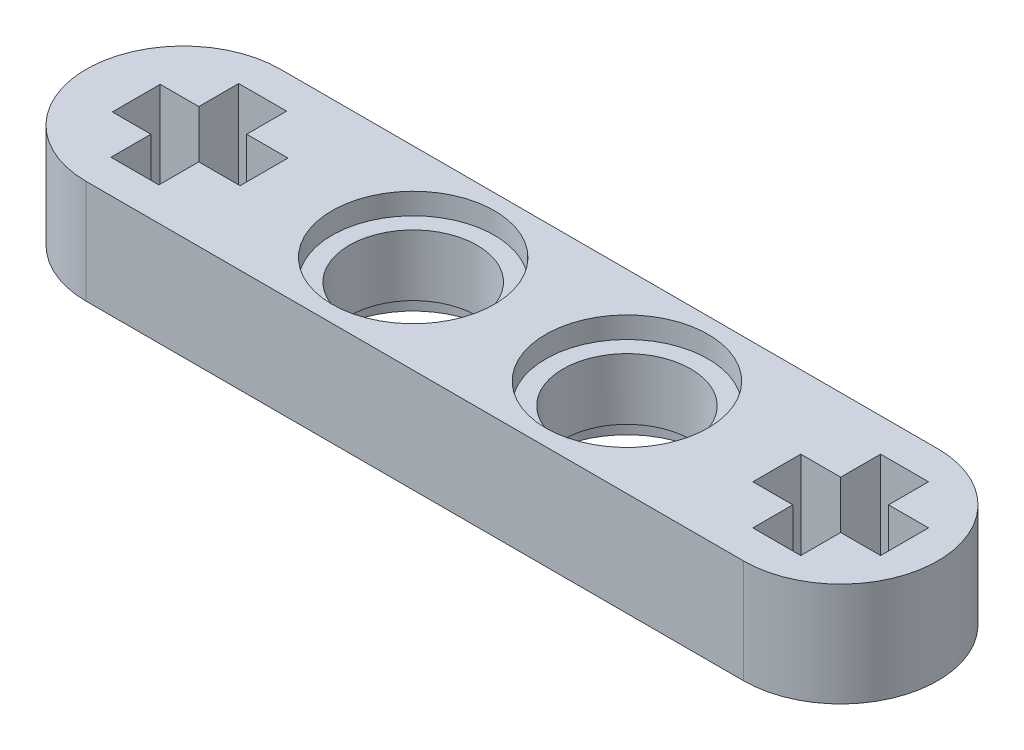
SolidWorks part; units mm, degrees
ref_plane "Front Plane" through (0, 0, 0) normal (0, 0, 1) x (1, 0, 0)
ref_plane "Top Plane" through (0, 0, 0) normal (0, 1, 0) x (1, 0, 0)
ref_plane "Right Plane" through (0, 0, 0) normal (1, 0, 0) x (0, 0, -1)
sketch "Sketch1" plane through (0, 0, 0) normal (0, 1, 0) x (1, 0, 0)
  line L0 (-12.665, 0) -> (12.035, 0) construction
  line L1 (-55, 0) -> (55, 0) construction
  line L2 (-12.665, 3.65) -> (12.035, 3.65)
  line L3 (-12.665, -3.65) -> (12.035, -3.65)
  line L4 (-16.315, 0) -> (-16.315, -5.5699) construction
  line L5 (-14.435, 0) -> (-14.435, -5.5699) construction
  line L6 (11.135, 2.4) -> (11.135, 0.9)
  line L7 (11.135, 2.4) -> (12.935, 2.4)
  line L8 (11.135, -2.4) -> (12.935, -2.4)
  line L9 (12.935, 2.4) -> (12.935, 0.9)
  line L10 (11.135, 2.4) -> (12.935, -2.4) construction
  line L11 (11.135, -2.4) -> (12.935, 2.4) construction
  line L12 (14.435, -0.9) -> (12.935, -0.9)
  line L13 (14.435, -0.9) -> (14.435, 0.9)
  line L14 (9.635, -0.9) -> (9.635, 0.9)
  line L15 (14.435, 0.9) -> (12.935, 0.9)
  line L16 (14.435, -0.9) -> (9.635, 0.9) construction
  line L17 (9.635, -0.9) -> (14.435, 0.9) construction
  line L18 (11.135, 0.9) -> (9.635, 0.9)
  line L19 (11.135, -0.9) -> (9.635, -0.9)
  line L20 (11.135, -0.9) -> (11.135, -2.4)
  line L21 (12.935, -0.9) -> (12.935, -2.4)
  line L34 (-12.985, 2.4011) -> (-12.985, 0.9011)
  line L35 (-12.985, 2.4011) -> (-11.185, 2.4011)
  line L36 (-12.985, -2.3989) -> (-11.185, -2.3989)
  line L37 (-11.185, 2.4011) -> (-11.185, 0.9011)
  line L38 (-9.6331, -0.8989) -> (-11.185, -0.8989)
  line L39 (-9.6331, -0.8989) -> (-9.6331, 0.9011)
  line L40 (-14.4331, -0.8989) -> (-14.4331, 0.9011)
  line L41 (-9.6331, 0.9011) -> (-11.185, 0.9011)
  line L42 (-12.985, 0.9011) -> (-14.4331, 0.9011)
  line L43 (-12.985, -0.8989) -> (-14.4331, -0.8989)
  line L44 (-12.985, -0.8989) -> (-12.985, -2.3989)
  line L45 (-11.185, -0.8989) -> (-11.185, -2.3989)
  line L46 (-12.985, 0.9011) -> (-11.185, -0.8989) construction
  line L47 (-12.085, 0.0011) -> (-11.185, 0.9011) construction
  arc A0 (-12.665, 3.65) -> (-12.665, -3.65) centre (-12.665, 0) ccw
  arc A1 (12.035, -3.65) -> (12.035, 3.65) centre (12.035, 0) ccw
  circle A2 centre (-4.045, 0.018) radius 2.4
  circle A3 centre (3.995, 0.0083) radius 2.4
  point P5 (-0.315, 0)
  point P17 (12.035, 0)
  point P18 (12.035, 0)
  dimension "D3" = 8.04
  dimension "D5" = 1.8
  dimension "D9" = 8.04
  dimension "D1" = 7.3
  dimension "D2" = 32
  dimension "D4" = 8.04
  dimension "D6" = 1.8
extrude "Boss-Extrude1" add sketch "Sketch1" along normal blind 3.9
sketch "Sketch2" plane through (0, 3.9, 0) normal (0, 1, 0) x (1, 0, 0)
  circle A0 centre (-4.045, 0.018) radius 3.05
  circle A1 centre (3.995, 0.0083) radius 3.05
extrude "Cut-Extrude1" cut sketch "Sketch2" against normal blind 0.8
sketch "Sketch3" plane through (0, 0, 0) normal (0, -1, 0) x (1, 0, 0)
  circle A0 centre (3.995, -0.0083) radius 3.05
  circle A1 centre (-4.045, -0.018) radius 3.05
extrude "Cut-Extrude2" cut sketch "Sketch3" against normal blind 0.8
